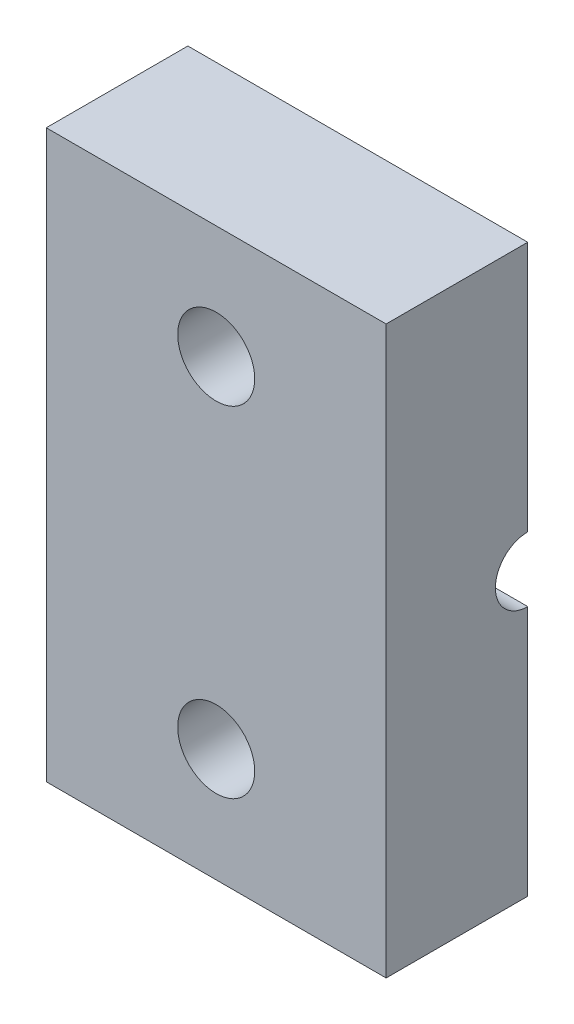
SolidWorks part; units mm, degrees
ref_plane "Front Plane" through (0, 0, 0) normal (0, 0, 1) x (1, 0, 0)
ref_plane "Top Plane" through (0, 0, 0) normal (0, 1, 0) x (1, 0, 0)
ref_plane "Right Plane" through (0, 0, 0) normal (1, 0, 0) x (0, 0, -1)
sketch "Sketch1" plane through (0, 0, 0) normal (0, 0, 1) x (1, 0, 0)
  line L0 (0, 12.7) -> (0, -12.7) construction
  line L1 (7.62, -12.7) -> (-7.62, -12.7)
  line L2 (7.62, -12.7) -> (7.62, 12.7)
  line L3 (7.62, 12.7) -> (-7.62, 12.7)
  line L4 (-7.62, -12.7) -> (-7.62, 12.7)
  line L5 (7.62, -12.7) -> (-7.62, 12.7) construction
  line L6 (7.62, 12.7) -> (-7.62, -12.7) construction
  point P0 (0, 0)
  dimension "D1" = 25.4
  dimension "D2" = 15.24
extrude "Boss-Extrude1" add sketch "Sketch1" along normal blind 6.35
hole_wizard "#29 (0.136) Diameter Hole1" positions "Sketch4" profile "Sketch5" hole size "#29" standard "ANSI Inch" end condition through all
sketch "Sketch4" plane through (0, 0, 6.35) normal (0, 0, 1) x (1, 0, 0)
  line L0 (0, 12.7) -> (0, -12.7) construction
  line L1 (7.62, 12.7) -> (-7.62, 12.7) construction
  line L2 (-7.62, -12.7) -> (7.62, -12.7) construction
  point P9 (0, 7.62)
  point P11 (0, -7.62)
  dimension "D1" = 5.08
  dimension "D2" = 5.08
sketch "Sketch5" plane through (0, -7.62, 6.35) normal (1, 0, 0) x (0, -1, 0)
  line L0 (0, 0) -> (0, 6.35)
  line L1 (0, 6.35) -> (1.7272, 6.35)
  line L2 (1.7272, 6.35) -> (1.7272, 0)
  line L5 (1.7272, 0) -> (0, 0)
  line L11 (0, -6.35) -> (0, 107.95) construction
  dimension "Thru Hole Dia." = 3.4544
  dimension "Thru Hole Depth" = 6.35
sketch "Sketch6" plane through (-7.62, 0, 0) normal (-1, 0, 0) x (0, 0, 1)
  line L0 (0, 12.7) -> (0, -12.7) construction
  circle A0 centre (0, 0) radius 1.45
  dimension "D1" = 2.9
extrude "Cut-Extrude1" cut sketch "Sketch6" against normal through all
